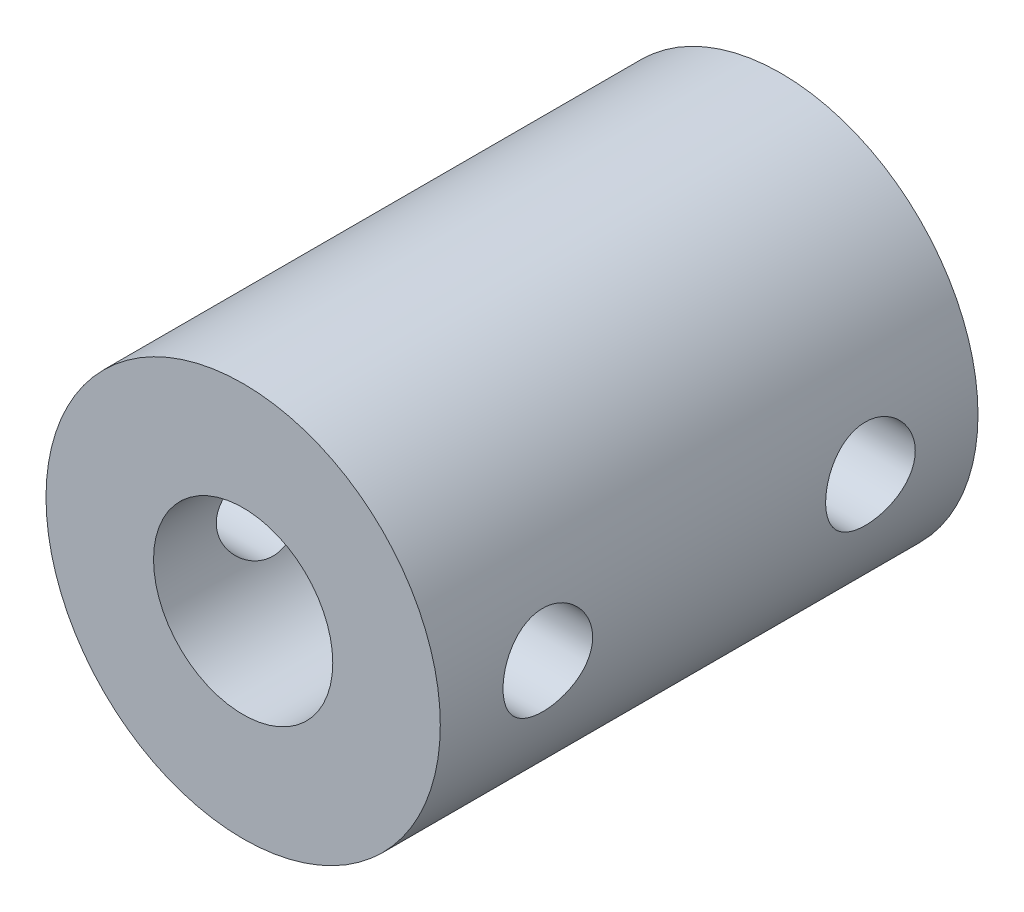
SolidWorks part; units mm, degrees
material "Латунь"
ref_plane "Спереди" through (0, 0, 0) normal (0, 0, 1) x (1, 0, 0)
ref_plane "Сверху" through (0, 0, 0) normal (0, 1, 0) x (1, 0, 0)
ref_plane "Справа" through (0, 0, 0) normal (1, 0, 0) x (0, 0, -1)
sketch "Эскиз1" plane through (0, 0, 0) normal (0, 0, 1) x (1, 0, 0)
  circle A0 centre (0, 0) radius 5.5
  circle A1 centre (0, 0) radius 2.5
  dimension "D1" = 5
  dimension "D2" = 11
extrude "Бобышка-Вытянуть1" add sketch "Эскиз1" along normal blind 15
ref_plane "Плоскость1" through (-5.5, 0, 0) normal (-1, 0, 0) x (0, 0, 1)
sketch "Эскиз2" plane through (-5.5, 0, 0) normal (-1, 0, 0) x (0, 0, 1)
  line L0 (0, 0) -> (15, 0) construction
  line L1 (15, -5.5) -> (15, 5.5) construction
  line L2 (0, 5.5) -> (0, -5.5) construction
  circle A0 centre (3, 0) radius 2 construction
  circle A1 centre (12, 0) radius 2 construction
  dimension "D1" = 4
  dimension "D2" = 4
  dimension "D3" = 3
  dimension "D4" = 3
hole_wizard "Отверстие обработанное метчиком M31" positions "Эскиз5" profile "Эскиз4" tap size "M3" standard "DIN" end condition through all
sketch "Эскиз5" plane through (-5.5, 0, 0) normal (-1, 0, 0) x (0, 0, 1)
  point P0 (12, 0)
  point P3 (3, 0)
sketch "Эскиз4" plane through (-5.5, 0, 12) normal (0, 1, 0) x (0, 0, 1)
  line L0 (0, 0) -> (0, 11)
  line L1 (0, 11) -> (1.25, 11)
  line L2 (1.25, 11) -> (1.25, 0)
  line L5 (1.25, 0) -> (0, 0)
  line L11 (0, -6.35) -> (0, 107.95) construction
  dimension "Диаметр проходного сверла" = 2.5
  dimension "Глубина проходного сверла" = 11
cosmetic thread "Отверстие резьбы3" parameters "D2"=3
cosmetic thread "Отверстие резьбы4" parameters "D2"=3
